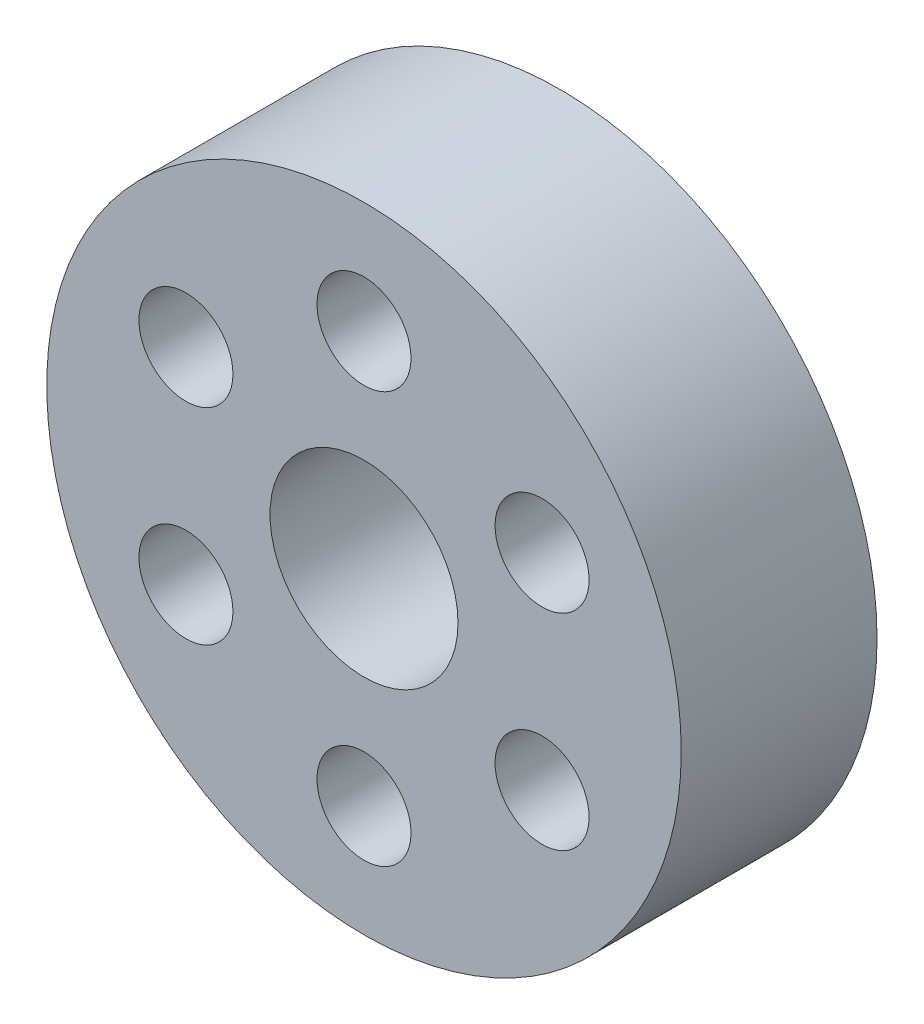
SolidWorks part; units mm, degrees
ref_plane "Front Plane" through (0, 0, 0) normal (0, 0, 1) x (1, 0, 0)
ref_plane "Top Plane" through (0, 0, 0) normal (0, 1, 0) x (1, 0, 0)
ref_plane "Right Plane" through (0, 0, 0) normal (1, 0, 0) x (0, 0, -1)
sketch "Sketch1" plane through (0, 0, 0) normal (0, 0, 1) x (1, 0, 0)
  circle A0 centre (0, 0) radius 1.524
  circle A1 centre (0, 0) radius 5.1435
  dimension "D1" = 3.048
  dimension "D2" = 3.6195
extrude "Boss-Extrude1" add sketch "Sketch1" along normal blind 3.175
sketch "Sketch2" plane through (0, 0, 3.175) normal (0, 0, 1) x (1, 0, 0)
  line L0 (0, 1.524) -> (0, 5.1435) construction
  circle A0 centre (0, 3.3337) radius 0.762
  circle A1 centre (0, 0) radius 1.524 construction
  circle A2 centre (0, 0) radius 5.1435 construction
  dimension "D1" = 1.524
extrude "Cut-Extrude1" cut sketch "Sketch2" against normal up to next (3.175 mm away)
pattern_circular "CirPattern1" count 6 over 360 about axis through (0, 0, 0) along (0, 0, 1) of "Cut-Extrude1"
